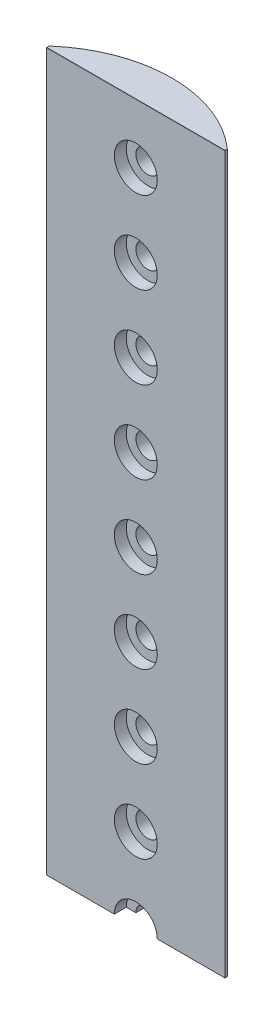
SolidWorks part; units mm, degrees
material "Plain Carbon Steel"
ref_plane "Front Plane" through (0, 0, 0) normal (0, 0, 1) x (1, 0, 0)
ref_plane "Top Plane" through (0, 0, 0) normal (0, 1, 0) x (1, 0, 0)
ref_plane "Right Plane" through (0, 0, 0) normal (1, 0, 0) x (0, 0, -1)
sketch "Sketch1" plane through (0, 0, 0) normal (0, 0, 1) x (1, 0, 0)
  line L1 (0, 0) -> (29.845, 0)
  line L2 (0, 0) -> (0, 120)
  line L3 (0, 120) -> (29.845, 120)
  line L4 (29.845, 0) -> (29.845, 120)
  dimension "D1" = 29.845
  dimension "D2" = 120
extrude "Boss-Extrude1" add sketch "Sketch1" along normal blind 0.4
sketch "Sketch3" plane through (0, 120, 0) normal (0, 1, 0) x (1, 0, 0)
  line L0 (29.845, 0) -> (0, 0) construction
  line L1 (29.845, 0) -> (0, 0)
  arc A0 (0, 0) -> (29.845, 0) centre (14.9225, -16.8605) cw
  dimension "D1" = 22.5157
extrude "Boss-Extrude2" add sketch "Sketch3" against normal through all
sketch "Sketch2" plane through (0, 0, 0.4) normal (0, 0, 1) x (1, 0, 0)
  line L0 (14.9225, 120) -> (14.9225, 0) construction
  line L1 (29.845, 120) -> (0, 120) construction
  line L2 (0, 0) -> (29.845, 0) construction
  circle A0 centre (14.9225, 0) radius 1.9844
  dimension "D1" = 3.9688
extrude "Cut-Extrude1" cut sketch "Sketch2" against normal through all
pattern_linear "LPattern1" count 15 spacing 13.75 along (0, 1, 0) of "Cut-Extrude1"
ref_plane "Plane1" through (0, 119.9, 0) normal (0, 1, 0) x (1, 0, 0)
split line "Split Line1"
sketch "Sketch4" plane through (0, 0, 0.4) normal (0, 0, 1) x (1, 0, 0)
  circle A0 centre (14.9225, 0) radius 3.5941
  dimension "D1" = 7.1882
extrude "Cut-Extrude2" cut sketch "Sketch4" along a picked direction on the side against the normal blind 2
pattern_linear "LPattern2" count 10 spacing 13.75 along (0, 1, 0) of "Cut-Extrude2"
